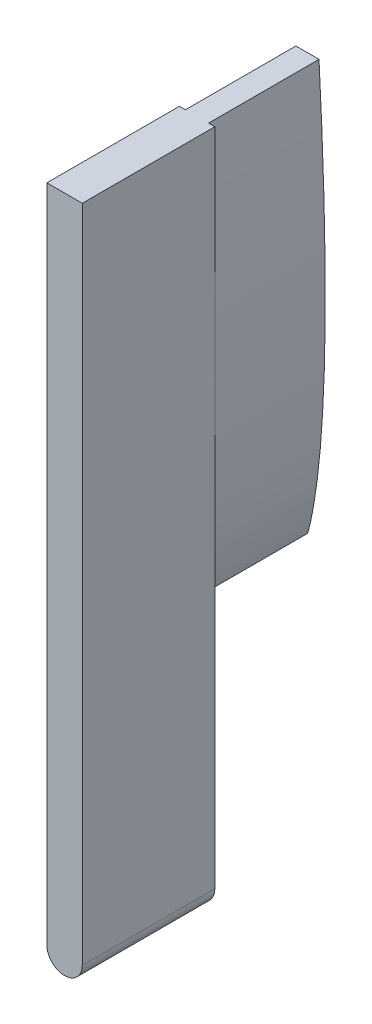
SolidWorks part; units mm, degrees
ref_plane "Front Plane" through (0, 0, 0) normal (0, 0, 1) x (1, 0, 0)
ref_plane "Top Plane" through (0, 0, 0) normal (0, 1, 0) x (1, 0, 0)
ref_plane "Right Plane" through (0, 0, 0) normal (1, 0, 0) x (0, 0, -1)
sketch "Sketch2" plane through (0, 0, 24.6313) normal (0, 0, -1) x (-1, 0, 0)
  line L0 (1.8231, 603) -> (1.8231, 663) construction
  line L1 (-1.8829, 663) -> (1.8231, 663) construction
  line L2 (-1.8829, 663) -> (-1.8829, 603) construction
  line L3 (1.8231, 603) -> (1.8231, 663)
  line L4 (-1.8829, 663) -> (1.8231, 663)
  line L5 (-1.8829, 663) -> (-1.8829, 603)
  arc A0 (-1.8829, 603) -> (1.8231, 603) centre (-0.0299, 603) ccw construction
  arc A1 (-1.8829, 603) -> (1.8231, 603) centre (-0.0299, 603) ccw
extrude "Boss-Extrude1" add sketch "Sketch2" against normal blind 12
sketch "Sketch3" plane through (0, 0, 24.6313) normal (0, 0, -1) x (-1, 0, 0)
  line L0 (1.2649, 663) -> (-1.3037, 663)
  spline S0 degree 3 poles (-1961.8066, 843.7044) (149.4668, 1066.229) (5.8444, 858.7241) (-1.8074, 651.5722) (-1.8966, 645.3725) (-1.869, 640.7329) (-1.7455, 636.8747) (-1.5621, 633.8055) (-1.3718, 631.5147) (-1.1106, 629.2463) (-0.8201, 627.377) (-0.5245, 625.9199) (3.3132, 610.8549) (25.7612, 631.2457) (312.5555, 2598.9915) knots -3.364041 -3.364041 -3.364041 -3.364041 0.664641 0.726374 0.75724 0.788106 0.818973 0.834406 0.849839 0.865272 0.880705 0.888422 0.896138 1.216024 1.216024 1.216024 1.216024 only from (-1.3037, 663) to (-0.0414, 624.2904) construction
  spline S1 degree 3 poles (-1.3037, 663) (-1.3702, 661.7766) (-1.5903, 657.4497) (-1.8074, 651.5722) (-1.8966, 645.3725) (-1.869, 640.7329) (-1.7455, 636.8747) (-1.5621, 633.8055) (-1.3718, 631.5147) (-1.1106, 629.2463) (-0.8201, 627.377) (-0.5245, 625.9199) (-0.2901, 625) (-0.1158, 624.48) (-0.0414, 624.2904) knots 0.640307 0.640307 0.640307 0.640307 0.664641 0.726374 0.75724 0.788106 0.818973 0.834406 0.849839 0.865272 0.880705 0.888422 0.896138 0.901181 0.901181 0.901181 0.901181
  spline S2 degree 3 poles (-310.4678, 2599.9057) (-25.8403, 631.2789) (-3.4118, 610.8574) (0.4434, 625.9193) (0.7407, 627.3761) (1.0333, 629.245) (1.2971, 631.5132) (1.49, 633.8038) (1.677, 636.8727) (1.8049, 640.7308) (1.8377, 645.3704) (1.7556, 651.5701) (-5.66, 858.7312) (-149.0465, 1066.4003) (1961.9901, 841.4659) knots 0.201656 0.201656 0.201656 0.201656 0.521572 0.529289 0.537005 0.552439 0.567872 0.583305 0.598738 0.629604 0.660471 0.691337 0.75307 4.781763 4.781763 4.781763 4.781763 only from (-0.0414, 624.2904) to (1.2649, 663) construction
  spline S3 degree 3 poles (-0.0414, 624.2904) (0.0331, 624.4799) (0.2081, 624.9997) (0.4434, 625.9193) (0.7407, 627.3761) (1.0333, 629.245) (1.2971, 631.5132) (1.49, 633.8038) (1.677, 636.8727) (1.8049, 640.7308) (1.8377, 645.3704) (1.7556, 651.5701) (1.5451, 657.4484) (1.33, 661.7761) (1.2649, 663) knots 0.51653 0.51653 0.51653 0.51653 0.521572 0.529289 0.537005 0.552439 0.567872 0.583305 0.598738 0.629604 0.660471 0.691337 0.75307 0.777414 0.777414 0.777414 0.777414
extrude "Boss-Extrude2" add sketch "Sketch3" along normal blind 10
sketch "Sketch4" plane through (0, 0, 14.6313) normal (0, 0, -1) x (-1, 0, 0)
  line L2 (1.0278, 662.75) -> (-1.0669, 662.75)
  line L3 (1.0278, 662.75) -> (-1.0669, 662.75)
  line L4 (5.702, 620.6235) -> (-8.0497, 620.6235)
  line L5 (5.702, 620.6235) -> (5.702, 666.9897)
  line L6 (5.702, 666.9897) -> (-8.0497, 666.9897)
  line L7 (-8.0497, 620.6235) -> (-8.0497, 666.9897)
  spline S4 degree 3 poles (-3877.5795, 1462.7047) (204.9338, 1073.5402) (5.3582, 867.5455) (-1.5797, 650.1569) (-1.6406, 647.0065) (-1.6278, 642.2801) (-1.606, 640.7044) (-1.5158, 637.5586) (-1.4473, 635.9878) (-1.242, 632.8525) (-1.1052, 631.2879) (-0.8074, 628.9495) (-0.6935, 628.1714) (-0.4871, 627.0074) (-0.4126, 626.6199) (5.5775, 598.9666) (54.0596, 575.5777) (3988.6099, 906.1314) knots -16.755971 -16.755971 -16.755971 -16.755971 0.25 0.25 0.5 0.5 0.625 0.625 0.75 0.75 0.875 0.875 0.9375 0.9375 0.96875 0.96875 3.172645 3.172645 3.172645 3.172645 only from (-1.0669, 662.75) to (-0.041, 625.0768)
  spline S5 degree 3 poles (-3981.2605, 999.9103) (-54.4965, 576.4475) (-5.7142, 598.8768) (0.3315, 626.6153) (0.4063, 627.002) (0.614, 628.1642) (0.7288, 628.9417) (1.0295, 631.2792) (1.1683, 632.8446) (1.3777, 635.9833) (1.448, 637.5573) (1.5419, 640.707) (1.5654, 642.2819) (1.5836, 647.0068) (1.5262, 650.1576) (-5.1671, 867.6193) (-204.6309, 1074.4483) (3880.6016, 1447.5271) knots -2.185043 -2.185043 -2.185043 -2.185043 0.03125 0.03125 0.0625 0.0625 0.125 0.125 0.25 0.25 0.375 0.375 0.5 0.5 0.75 0.75 17.763413 17.763413 17.763413 17.763413 only from (-0.041, 625.0768) to (1.0278, 662.75)
  spline S6 degree 3 poles (-1.0669, 662.75) (-1.2365, 659.6035) (-1.3787, 656.4558) (-1.5797, 650.1569) (-1.6406, 647.0065) (-1.6278, 642.2801) (-1.606, 640.7044) (-1.5158, 637.5586) (-1.4473, 635.9878) (-1.242, 632.8525) (-1.1052, 631.2879) (-0.8074, 628.9495) (-0.6935, 628.1714) (-0.4871, 627.0074) (-0.4126, 626.6199) (-0.2451, 625.8467) (-0.1528, 625.4608) (-0.041, 625.0768) knots 0 0 0 0 0.25 0.25 0.5 0.5 0.625 0.625 0.75 0.75 0.875 0.875 0.9375 0.9375 0.96875 0.96875 1 1 1 1
  spline S7 degree 3 poles (-0.041, 625.0768) (0.0708, 625.4592) (0.1634, 625.8439) (0.3315, 626.6153) (0.4063, 627.002) (0.614, 628.1642) (0.7288, 628.9417) (1.0295, 631.2792) (1.1683, 632.8446) (1.3777, 635.9833) (1.448, 637.5573) (1.5419, 640.707) (1.5654, 642.2819) (1.5836, 647.0068) (1.5262, 650.1576) (1.3324, 656.456) (1.1938, 659.6035) (1.0278, 662.75) knots 0 0 0 0 0.03125 0.03125 0.0625 0.0625 0.125 0.125 0.25 0.25 0.375 0.375 0.5 0.5 0.75 0.75 1 1 1 1
  dimension "D1" = 0.25
extrude "Cut-Extrude1" cut sketch "Sketch4" against normal up to surface (10 mm away) up to face at (0.4028, 623.4851, 24.6313)
sketch "Sketch5" plane through (0, 0, 36.6313) normal (0, 0, 1) x (1, 0, 0)
  line L4 (-4.1227, 664.9968) -> (4.1608, 664.9968)
  line L5 (-4.1227, 664.9968) -> (-4.1227, 599.0782)
  line L6 (1.6329, 603) -> (1.6329, 662.75)
  line L7 (1.6329, 662.75) -> (-1.5731, 662.75)
  line L8 (-1.5731, 662.75) -> (-1.5731, 603)
  line L9 (1.6329, 603) -> (1.6329, 662.75)
  line L10 (1.6329, 662.75) -> (-1.5731, 662.75)
  line L11 (-1.5731, 662.75) -> (-1.5731, 603)
  line L12 (-4.1227, 599.0782) -> (4.1608, 599.0782)
  line L13 (4.1608, 664.9968) -> (4.1608, 599.0782)
  arc A2 (-1.5731, 603) -> (1.6329, 603) centre (0.0299, 603) ccw
  arc A3 (-1.5731, 603) -> (1.6329, 603) centre (0.0299, 603) ccw
  dimension "D1" = 0.25
extrude "Cut-Extrude2" cut sketch "Sketch5" against normal up to surface (12 mm away) up to face at (0.0299, 632.5368, 24.6313)
